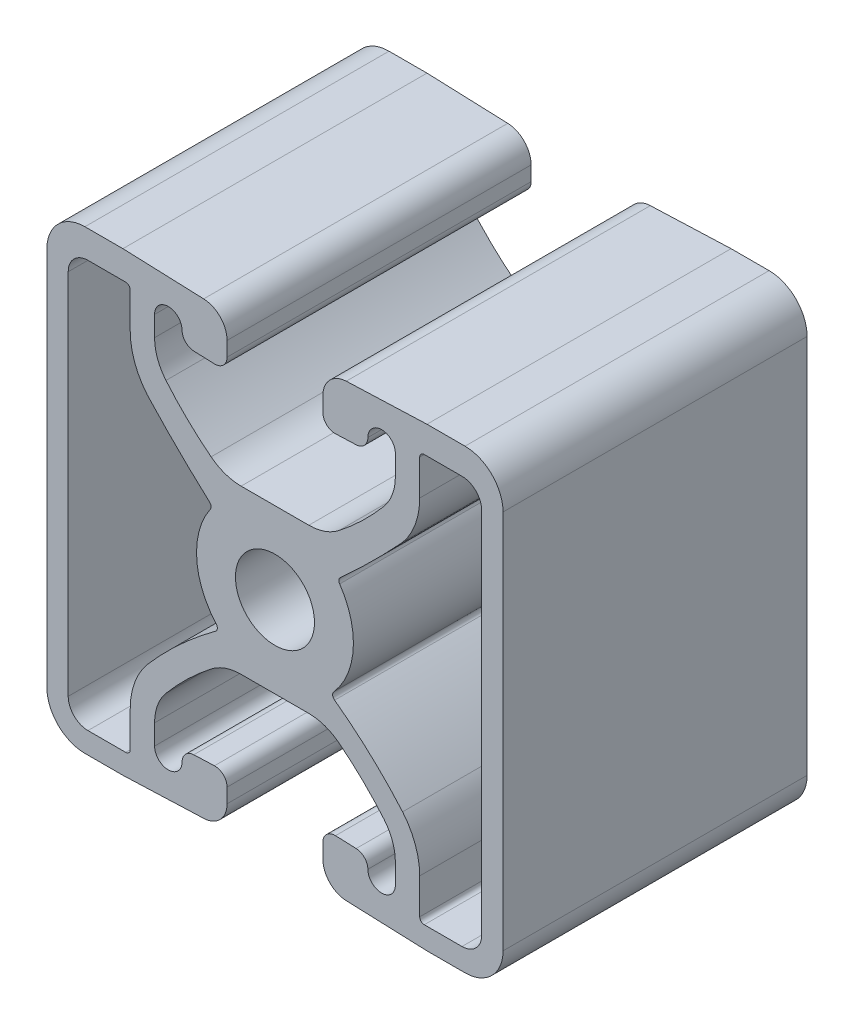
SolidWorks part; units mm, degrees
material "6061 Alloy"
ref_plane "Front" through (0, 0, 0) normal (0, 0, 1) x (1, 0, 0)
ref_plane "Top" through (0, 0, 0) normal (0, 1, 0) x (1, 0, 0)
ref_plane "Right" through (0, 0, 0) normal (1, 0, 0) x (0, 0, -1)
sketch "Sketch1" plane through (0, 0, 0) normal (0, 0, 1) x (1, 0, 0)
  line L0 (119.2865, 134.9615) -> (116.4584, 134.9615)
  line L1 (113.6303, 134.9615) -> (116.4584, 134.9615)
  line L2 (126.5168, 142.086) -> (126.5168, 143.769)
  line L3 (106.4, 142.086) -> (106.4, 143.769)
  line L4 (123.2411, 142.7575) -> (121.5139, 142.6912)
  line L5 (109.6757, 142.7575) -> (111.4029, 142.6912)
  line L6 (120.4589, 143.7064) -> (120.4589, 144.9147)
  line L7 (112.4579, 143.7064) -> (112.4579, 144.9147)
  line L8 (129.1584, 147.2043) -> (122.4129, 146.9452)
  line L9 (103.7584, 147.2043) -> (110.5039, 146.9452)
  line L10 (132.3334, 147.2043) -> (129.1584, 147.2043)
  line L11 (100.5834, 147.2043) -> (103.7584, 147.2043)
  line L12 (135.5084, 144.0293) -> (135.5084, 112.2793)
  line L13 (97.4084, 144.0293) -> (97.4084, 112.2793)
  line L14 (132.3334, 109.1043) -> (129.1584, 109.1043)
  line L15 (100.5834, 109.1043) -> (103.7584, 109.1043)
  line L16 (129.1584, 109.1043) -> (122.4129, 109.3635)
  line L17 (103.7584, 109.1043) -> (110.5039, 109.3635)
  line L18 (120.4589, 112.6023) -> (120.4589, 111.394)
  line L19 (112.4579, 112.6023) -> (112.4579, 111.394)
  line L20 (123.2411, 113.5512) -> (121.5139, 113.6175)
  line L21 (109.6757, 113.5512) -> (111.4029, 113.6175)
  line L22 (126.5168, 114.2227) -> (126.5168, 112.5397)
  line L23 (106.4, 114.2227) -> (106.4, 112.5397)
  line L24 (119.2865, 121.3471) -> (116.4584, 121.3471)
  line L25 (113.6303, 121.3471) -> (116.4584, 121.3471)
  line L26 (128.5488, 141.5599) -> (128.5488, 144.5193)
  line L27 (132.0794, 144.9003) -> (128.9298, 144.9003)
  line L28 (133.7304, 143.2493) -> (133.7304, 112.5333)
  line L29 (128.5488, 114.2227) -> (128.5488, 111.2633)
  line L30 (132.0794, 110.8823) -> (128.9298, 110.8823)
  line L31 (104.368, 141.5599) -> (104.368, 144.5193)
  line L32 (100.8374, 144.9003) -> (103.987, 144.9003)
  line L33 (99.1864, 143.2493) -> (99.1864, 112.5333)
  line L34 (100.8374, 110.8823) -> (103.987, 110.8823)
  line L35 (104.368, 114.2227) -> (104.368, 111.2633)
  arc A0 (119.2865, 134.9615) -> (121.7943, 135.8276) centre (119.2865, 139.0255) ccw
  arc A1 (111.1226, 135.8276) -> (113.6303, 134.9615) centre (113.6303, 139.0255) ccw
  arc A2 (121.7943, 135.8276) -> (125.5637, 139.4709) centre (106.1206, 155.8149) ccw
  arc A3 (107.3531, 139.4709) -> (111.1226, 135.8276) centre (126.7962, 155.8149) ccw
  arc A4 (125.5637, 139.4709) -> (126.5168, 142.086) centre (122.4528, 142.086) ccw
  arc A5 (106.4, 142.086) -> (107.3531, 139.4709) centre (110.464, 142.086) ccw
  arc A6 (126.5168, 143.769) -> (124.2181, 143.771) centre (125.3675, 143.769) ccw
  arc A7 (108.6987, 143.771) -> (106.4, 143.769) centre (107.5494, 143.769) ccw
  arc A8 (123.2411, 142.7575) -> (124.2181, 143.771) centre (123.2021, 143.7728) ccw
  arc A9 (108.6987, 143.771) -> (109.6757, 142.7575) centre (109.7147, 143.7728) ccw
  arc A10 (120.4589, 143.7064) -> (121.5139, 142.6912) centre (121.4749, 143.7064) ccw
  arc A11 (111.4029, 142.6912) -> (112.4579, 143.7064) centre (111.4419, 143.7064) ccw
  arc A12 (122.4129, 146.9452) -> (120.4589, 144.9147) centre (122.4909, 144.9147) ccw
  arc A13 (112.4579, 144.9147) -> (110.5039, 146.9452) centre (110.4259, 144.9147) ccw
  arc A14 (135.5084, 144.0293) -> (132.3334, 147.2043) centre (132.3334, 144.0293) ccw
  arc A15 (100.5834, 147.2043) -> (97.4084, 144.0293) centre (100.5834, 144.0293) ccw
  arc A16 (132.3334, 109.1043) -> (135.5084, 112.2793) centre (132.3334, 112.2793) ccw
  arc A17 (97.4084, 112.2793) -> (100.5834, 109.1043) centre (100.5834, 112.2793) ccw
  arc A18 (120.4589, 111.394) -> (122.4129, 109.3635) centre (122.4909, 111.394) ccw
  arc A19 (110.5039, 109.3635) -> (112.4579, 111.394) centre (110.4259, 111.394) ccw
  arc A20 (121.5139, 113.6175) -> (120.4589, 112.6023) centre (121.4749, 112.6023) ccw
  arc A21 (112.4579, 112.6023) -> (111.4029, 113.6175) centre (111.4419, 112.6023) ccw
  arc A22 (124.2181, 112.5377) -> (123.2411, 113.5512) centre (123.2021, 112.5359) ccw
  arc A23 (109.6757, 113.5512) -> (108.6987, 112.5377) centre (109.7147, 112.5359) ccw
  arc A24 (124.2181, 112.5377) -> (126.5168, 112.5397) centre (125.3675, 112.5397) ccw
  arc A25 (106.4, 112.5397) -> (108.6987, 112.5377) centre (107.5494, 112.5397) ccw
  arc A26 (126.5168, 114.2227) -> (125.5637, 116.8377) centre (122.4528, 114.2227) ccw
  arc A27 (107.3531, 116.8377) -> (106.4, 114.2227) centre (110.464, 114.2227) ccw
  arc A28 (125.5637, 116.8377) -> (121.7943, 120.4811) centre (106.1206, 100.4937) ccw
  arc A29 (111.1226, 120.4811) -> (107.3531, 116.8377) centre (126.7962, 100.4937) ccw
  arc A30 (121.7943, 120.4811) -> (119.2865, 121.3471) centre (119.2865, 117.2831) ccw
  arc A31 (113.6303, 121.3471) -> (111.1226, 120.4811) centre (113.6303, 117.2831) ccw
  arc A32 (127.1192, 137.6374) -> (128.5488, 141.5599) centre (122.4528, 141.5599) ccw
  arc A33 (121.9073, 132.4832) -> (127.1192, 137.6374) centre (68.928, 191.2671) ccw
  arc A34 (121.9073, 132.4832) -> (121.8626, 131.9982) centre (122.1767, 132.2138) ccw
  arc A35 (128.9298, 144.9003) -> (128.5488, 144.5193) centre (128.9298, 144.5193) ccw
  arc A36 (121.37, 123.9532) -> (121.8626, 131.9982) centre (116.4584, 128.2915) ccw
  arc A37 (121.37, 123.9532) -> (121.4428, 123.385) centre (121.6556, 123.701) ccw
  arc A38 (133.7304, 143.2493) -> (132.0794, 144.9003) centre (132.0794, 143.2493) ccw
  arc A39 (127.1192, 118.1452) -> (121.4428, 123.385) centre (100.9704, 95.5117) ccw
  arc A40 (128.5488, 114.2227) -> (127.1192, 118.1452) centre (122.4528, 114.2227) ccw
  arc A41 (132.0794, 110.8823) -> (133.7304, 112.5333) centre (132.0794, 112.5333) ccw
  arc A42 (128.5488, 111.2633) -> (128.9298, 110.8823) centre (128.9298, 111.2633) ccw
  arc A43 (104.368, 141.5599) -> (105.7977, 137.6374) centre (110.464, 141.5599) ccw
  arc A44 (105.7977, 137.6374) -> (111.0095, 132.4832) centre (163.9889, 191.2671) ccw
  arc A45 (104.368, 144.5193) -> (103.987, 144.9003) centre (103.987, 144.5193) ccw
  arc A46 (111.0543, 131.9982) -> (111.0095, 132.4832) centre (110.7401, 132.2138) ccw
  arc A47 (111.0543, 131.9982) -> (111.5469, 123.9532) centre (116.4584, 128.2915) ccw
  arc A48 (100.8374, 144.9003) -> (99.1864, 143.2493) centre (100.8374, 143.2493) ccw
  arc A49 (111.4741, 123.385) -> (111.5469, 123.9532) centre (111.2613, 123.701) ccw
  arc A50 (111.4741, 123.385) -> (105.7977, 118.1452) centre (131.9465, 95.5117) ccw
  arc A51 (99.1864, 112.5333) -> (100.8374, 110.8823) centre (100.8374, 112.5333) ccw
  arc A52 (105.7977, 118.1452) -> (104.368, 114.2227) centre (110.464, 114.2227) ccw
  arc A53 (103.987, 110.8823) -> (104.368, 111.2633) centre (103.987, 111.2633) ccw
  arc A54 (116.4584, 131.4563) -> (116.4584, 124.8523) centre (116.4584, 128.1543) ccw
  arc A55 (116.4584, 124.8523) -> (116.4584, 131.4563) centre (116.4584, 128.1543) ccw
extrude "Extrude1" add sketch "Sketch1" along normal blind 25.4
